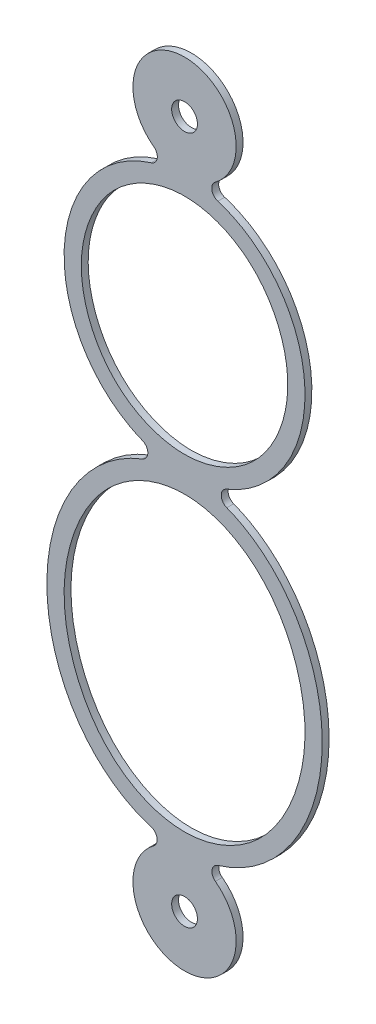
SolidWorks part; units mm, degrees
material "3.0517 (EN-AW 3003)"
ref_plane "Front Plane" through (0, 0, 0) normal (0, 0, 1) x (1, 0, 0)
ref_plane "Top Plane" through (0, 0, 0) normal (0, 1, 0) x (1, 0, 0)
ref_plane "Right Plane" through (0, 0, 0) normal (1, 0, 0) x (0, 0, -1)
sketch "Sketch1" plane through (0, 0, 0) normal (0, 0, 1) x (1, 0, 0)
  line L0 (0, 10) -> (0, -10) construction
  line L1 (-4, -3.75) -> (4, -3.75) construction
  line L2 (-3.5, 4.75) -> (3.5, 4.75) construction
  arc A0 (0.8919, 8.794) -> (-0.8919, 8.794) centre (0, 10) ccw
  circle A1 centre (0, 10) radius 0.375
  arc A2 (-0.8961, -8.7971) -> (0.8961, -8.7971) centre (0, -10) ccw
  circle A3 centre (0, -10) radius 0.375
  arc A4 (1.2236, 1.2366) -> (1.227, 0.771) centre (1.3164, 1.0045) ccw
  arc A5 (0.8919, 8.794) -> (0.967, 8.354) centre (1.0406, 8.593) ccw
  arc A6 (0.974, -8.357) -> (0.8961, -8.7971) centre (1.0455, -8.5966) ccw
  arc A7 (-0.967, 8.354) -> (-0.8919, 8.794) centre (-1.0406, 8.593) ccw
  arc A8 (-1.227, 0.771) -> (-1.2236, 1.2366) centre (-1.3164, 1.0045) ccw
  arc A9 (-0.8961, -8.7971) -> (-0.974, -8.357) centre (-1.0455, -8.5966) ccw
  ellipse E0 centre (0, -3.75) end of major axis (0, -8.5) minor radius 4 (0.974, -8.357) -> (1.227, 0.771) ccw
  ellipse E1 centre (0, 4.75) end of major axis (0, 8.5) minor radius 3.5 (1.2236, 1.2366) -> (0.967, 8.354) ccw
  ellipse E2 centre (0, -3.75) end of major axis (0, -8.5) minor radius 4 (-1.227, 0.771) -> (-0.974, -8.357) ccw
  ellipse E3 centre (0, 4.75) end of major axis (0, 8.5) minor radius 3.5 (-0.967, 8.354) -> (-1.2236, 1.2366) ccw
  spline S1 degree 3 poles (-2.3303, 2.182) (0, 1.159) (2.3303, 2.182) (3.3348, 4.75) (2.3303, 7.318) (0, 8.341) (-2.3303, 7.318) (-3.3348, 4.75) (-2.3303, 2.182) (0, 1.159) (2.3303, 2.182) knots -2.356194 -1.570796 -0.785398 0 0.785398 1.570796 2.356194 3.141593 3.926991 4.712389 5.497787 6.283185 7.068583 7.853982 8.63938 only from (0, 1.5) to (0, 1.5)
  spline S3 degree 3 poles (-2.6931, -7.1343) (0, -8.4328) (2.6931, -7.1343) (3.9035, -3.75) (2.6931, -0.3657) (0, 0.9328) (-2.6931, -0.3657) (-3.9035, -3.75) (-2.6931, -7.1343) (0, -8.4328) (2.6931, -7.1343) knots -2.356194 -1.570796 -0.785398 0 0.785398 1.570796 2.356194 3.141593 3.926991 4.712389 5.497787 6.283185 7.068583 7.853982 8.63938 only from (0, -8) to (0, -8)
  dimension "D2" = 3
  dimension "D3" = 0.75
  dimension "D4" = 8
  dimension "D5" = 7
  dimension "D8" = 0.5
  dimension "D1" = 20
  dimension "D6" = 1
extrude "Boss-Extrude1" add sketch "Sketch1" along normal mid plane 0.2
sketch "Sketch2" plane through (0, 0, 0) normal (0, 0, 1) x (1, 0, 0)
  arc A8 (-1.0406, 8.593) -> (1.0406, 8.593) centre (0, 5.2145) cw
  arc A9 (-1.0455, -8.5966) -> (1.0455, -8.5966) centre (0, -5.09) ccw
  arc A16 (-1.0455, -8.5966) -> (1.0455, -8.5966) centre (0, -10) ccw
  arc A17 (1.0406, 8.593) -> (-1.0406, 8.593) centre (0, 10) ccw
  spline S0 degree 3 poles (1903.9257, -3507.5478) (289.7163, -408.9287) (27.011, 29.4324) (-2.4572, 7.8021) (-2.7414, 7.5116) (-3.2192, 6.8444) (-3.4026, 6.4813) (-3.5971, 5.8993) (-3.6476, 5.7003) (-3.7192, 5.301) (-3.7405, 5.0994) (-3.7545, 4.6925) (-3.7467, 4.4861) (-3.7023, 4.0821) (-3.6658, 3.8829) (-3.5644, 3.4904) (-3.4988, 3.2957) (-3.3398, 2.9191) (-3.2473, 2.7387) (-3.0364, 2.3935) (-2.9181, 2.2287) (-2.6539, 1.9159) (-2.5096, 1.7702) (-2.2029, 1.5059) (-2.0396, 1.3864) (13.5785, -8.1674) (115.4937, 87.2895) (-2980.8985, 2665.0914) knots -10.874457 -10.874457 -10.874457 -10.874457 0.125 0.125 0.25 0.25 0.375 0.375 0.4375 0.4375 0.5 0.5 0.5625 0.5625 0.625 0.625 0.6875 0.6875 0.75 0.75 0.8125 0.8125 0.875 0.875 0.9375 0.9375 6.492725 6.492725 6.492725 6.492725 only from (-1.0406, 8.593) to (-1.3164, 1.0045)
  spline S1 degree 3 poles (2216.1793, -3327.1601) (203.0497, -213.2288) (19.6302, 20.3665) (-2.973, -0.1319) (-3.2868, -0.5343) (-3.7889, -1.4217) (-3.9705, -1.8927) (-4.2087, -2.8844) (-4.2605, -3.3865) (-4.2421, -4.1459) (-4.2194, -4.4012) (-4.1418, -4.9002) (-4.0871, -5.1457) (-3.9452, -5.6281) (-3.858, -5.8651) (-3.6481, -6.33) (-3.5276, -6.5527) (-3.2564, -6.9752) (-3.1056, -7.1755) (-2.7707, -7.5524) (-2.5844, -7.7304) (-2.1879, -8.0467) (-1.9773, -8.1861) (15.7469, -17.6181) (119.1337, 97.72) (-2852.0183, 2791.7154) knots -7.238931 -7.238931 -7.238931 -7.238931 0.125 0.125 0.25 0.25 0.375 0.375 0.5 0.5 0.5625 0.5625 0.625 0.625 0.6875 0.6875 0.75 0.75 0.8125 0.8125 0.875 0.875 0.9375 0.9375 5.819116 5.819116 5.819116 5.819116 only from (-1.3164, 1.0045) to (-1.0455, -8.5966)
  spline S2 degree 3 poles (-1859.3382, 3531.6341) (-167.8124, 210.1423) (-22.0845, -20.9335) (1.9694, -8.1909) (2.1831, -8.0501) (2.5809, -7.7337) (2.7638, -7.5594) (3.1007, -7.1819) (3.2553, -6.977) (3.5288, -6.5508) (3.6486, -6.3287) (3.8569, -5.8675) (3.9456, -5.627) (4.0882, -5.1415) (4.1427, -4.8954) (4.2198, -4.3968) (4.2424, -4.1429) (4.2603, -3.3812) (4.2079, -2.8811) (4.0306, -2.1426) (3.9542, -1.898) (3.7712, -1.4286) (3.6641, -1.2018) (3.2941, -0.546) (2.9766, -0.1369) (-14.3264, 15.6334) (-163.1414, -94.3327) (1669.742, -3628.5284) knots -6.625593 -6.625593 -6.625593 -6.625593 0.0625 0.0625 0.125 0.125 0.1875 0.1875 0.25 0.25 0.3125 0.3125 0.375 0.375 0.4375 0.4375 0.5 0.5 0.625 0.625 0.6875 0.6875 0.75 0.75 0.875 0.875 6.552625 6.552625 6.552625 6.552625 only from (1.0455, -8.5966) to (1.3164, 1.0045)
  spline S3 degree 3 poles (-2182.1089, 3351.3968) (-303.9875, 366.6085) (-24.3441, -21.3402) (2.666, 1.9046) (2.928, 2.216) (3.3554, 2.9155) (3.513, 3.2915) (3.6663, 3.8847) (3.7031, 4.0873) (3.747, 4.4908) (3.7545, 4.6933) (3.7405, 5.0996) (3.7187, 5.305) (3.6464, 5.7057) (3.5963, 5.9019) (3.4036, 6.478) (3.2157, 6.8492) (2.8625, 7.3425) (2.7324, 7.4979) (2.4461, 7.7894) (2.2905, 7.9244) (1.9639, 8.1643) (1.7917, 8.2706) (-14.334, 16.447) (-108.4577, -84.9417) (3192.8979, -2397.1321) knots -10.602344 -10.602344 -10.602344 -10.602344 0.125 0.125 0.25 0.25 0.375 0.375 0.4375 0.4375 0.5 0.5 0.5625 0.5625 0.625 0.625 0.75 0.75 0.8125 0.8125 0.875 0.875 0.9375 0.9375 6.428873 6.428873 6.428873 6.428873 only from (1.3164, 1.0045) to (1.0406, 8.593)
  spline S4 degree 3 poles (-1.0406, 8.593) (-1.4336, 8.4719) (-1.7949, 8.2882) (-2.4572, 7.8021) (-2.7414, 7.5116) (-3.2192, 6.8444) (-3.4026, 6.4813) (-3.5971, 5.8993) (-3.6476, 5.7003) (-3.7192, 5.301) (-3.7405, 5.0994) (-3.7545, 4.6925) (-3.7467, 4.4861) (-3.7023, 4.0821) (-3.6658, 3.8829) (-3.5644, 3.4904) (-3.4988, 3.2957) (-3.3398, 2.9191) (-3.2473, 2.7387) (-3.0364, 2.3935) (-2.9181, 2.2287) (-2.6539, 1.9159) (-2.5096, 1.7702) (-2.2029, 1.5059) (-2.0396, 1.3864) (-1.6921, 1.1738) (-1.5073, 1.0808) (-1.3164, 1.0045) knots 0 0 0 0 0.125 0.125 0.25 0.25 0.375 0.375 0.4375 0.4375 0.5 0.5 0.5625 0.5625 0.625 0.625 0.6875 0.6875 0.75 0.75 0.8125 0.8125 0.875 0.875 0.9375 0.9375 1 1 1 1
  spline S5 degree 3 poles (-1.3164, 1.0045) (-1.7947, 0.8214) (-2.2184, 0.5524) (-2.973, -0.1319) (-3.2868, -0.5343) (-3.7889, -1.4217) (-3.9705, -1.8927) (-4.2087, -2.8844) (-4.2605, -3.3865) (-4.2421, -4.1459) (-4.2194, -4.4012) (-4.1418, -4.9002) (-4.0871, -5.1457) (-3.9452, -5.6281) (-3.858, -5.8651) (-3.6481, -6.33) (-3.5276, -6.5527) (-3.2564, -6.9752) (-3.1056, -7.1755) (-2.7707, -7.5524) (-2.5844, -7.7304) (-2.1879, -8.0467) (-1.9773, -8.1861) (-1.5292, -8.4246) (-1.291, -8.5234) (-1.0455, -8.5966) knots 0 0 0 0 0.125 0.125 0.25 0.25 0.375 0.375 0.5 0.5 0.5625 0.5625 0.625 0.625 0.6875 0.6875 0.75 0.75 0.8125 0.8125 0.875 0.875 0.9375 0.9375 1 1 1 1
  spline S6 degree 3 poles (1.0455, -8.5966) (1.2906, -8.5235) (1.524, -8.4268) (1.9694, -8.1909) (2.1831, -8.0501) (2.5809, -7.7337) (2.7638, -7.5594) (3.1007, -7.1819) (3.2553, -6.977) (3.5288, -6.5508) (3.6486, -6.3287) (3.8569, -5.8675) (3.9456, -5.627) (4.0882, -5.1415) (4.1427, -4.8954) (4.2198, -4.3968) (4.2424, -4.1429) (4.2603, -3.3812) (4.2079, -2.8811) (4.0306, -2.1426) (3.9542, -1.898) (3.7712, -1.4286) (3.6641, -1.2018) (3.2941, -0.546) (2.9766, -0.1369) (2.2311, 0.5426) (1.7944, 0.8215) (1.3164, 1.0045) knots 0 0 0 0 0.0625 0.0625 0.125 0.125 0.1875 0.1875 0.25 0.25 0.3125 0.3125 0.375 0.375 0.4375 0.4375 0.5 0.5 0.625 0.625 0.6875 0.6875 0.75 0.75 0.875 0.875 1 1 1 1
  spline S7 degree 3 poles (1.3164, 1.0045) (1.6983, 1.1572) (2.0438, 1.3691) (2.666, 1.9046) (2.928, 2.216) (3.3554, 2.9155) (3.513, 3.2915) (3.6663, 3.8847) (3.7031, 4.0873) (3.747, 4.4908) (3.7545, 4.6933) (3.7405, 5.0996) (3.7187, 5.305) (3.6464, 5.7057) (3.5963, 5.9019) (3.4036, 6.478) (3.2157, 6.8492) (2.8625, 7.3425) (2.7324, 7.4979) (2.4461, 7.7894) (2.2905, 7.9244) (1.9639, 8.1643) (1.7917, 8.2706) (1.4288, 8.4546) (1.2372, 8.5324) (1.0406, 8.593) knots 0 0 0 0 0.125 0.125 0.25 0.25 0.375 0.375 0.4375 0.4375 0.5 0.5 0.5625 0.5625 0.625 0.625 0.75 0.75 0.8125 0.8125 0.875 0.875 0.9375 0.9375 1 1 1 1
  spline S10 degree 3 poles (0.1901, 7.75) (-0.1901, 7.75) (-0.3763, 7.7278) (-0.7417, 7.6436) (-0.9225, 7.5805) (-1.2624, 7.4203) (-1.4229, 7.3232) (-1.7248, 7.0946) (-1.8627, 6.9655) (-2.1087, 6.6828) (-2.2187, 6.5273) (-2.4077, 6.2012) (-2.4868, 6.0311) (-2.6162, 5.6776) (-2.6661, 5.4936) (-2.7326, 5.1251) (-2.75, 4.9389) (-2.75, 4.5625) (-2.7323, 4.3726) (-2.6655, 4.004) (-2.6164, 3.8232) (-2.4868, 3.4688) (-2.4066, 3.2968) (-2.2191, 2.9735) (-2.1113, 2.8206) (-1.8634, 2.5351) (-1.7248, 2.4056) (-1.4274, 2.18) (-1.2673, 2.0823) (-0.9238, 1.9198) (-0.7467, 1.8579) (-0.3817, 1.7731) (-0.1912, 1.7503) (0.1847, 1.7497) (0.3708, 1.7713) (0.7392, 1.8555) (0.9188, 1.9181) (1.2588, 2.0777) (1.4225, 2.1767) (1.7228, 2.4037) (1.8599, 2.5316) (2.1079, 2.816) (2.2179, 2.9716) (2.4065, 3.2965) (2.4866, 3.4681) (2.6165, 3.8235) (2.6656, 4.0046) (2.7324, 4.3735) (2.7501, 4.5633) (2.7499, 4.9403) (2.7324, 5.1266) (2.6657, 5.4951) (2.6157, 5.679) (2.4862, 6.0326) (2.4071, 6.2022) (2.219, 6.5267) (2.1085, 6.683) (1.8623, 6.9659) (1.7261, 7.0933) (1.428, 7.3196) (1.2641, 7.4193) (0.9247, 7.5796) (0.748, 7.6418) (0.3796, 7.7274) (0.1901, 7.75) (-0.1901, 7.75) (-0.3763, 7.7278) knots -0.03125 -0.03125 0 0 0.03125 0.03125 0.0625 0.0625 0.09375 0.09375 0.125 0.125 0.15625 0.15625 0.1875 0.1875 0.21875 0.21875 0.25 0.25 0.28125 0.28125 0.3125 0.3125 0.34375 0.34375 0.375 0.375 0.40625 0.40625 0.4375 0.4375 0.46875 0.46875 0.5 0.5 0.53125 0.53125 0.5625 0.5625 0.59375 0.59375 0.625 0.625 0.65625 0.65625 0.6875 0.6875 0.71875 0.71875 0.75 0.75 0.78125 0.78125 0.8125 0.8125 0.84375 0.84375 0.875 0.875 0.90625 0.90625 0.9375 0.9375 0.96875 0.96875 1 1 1.03125 1.03125 1.0625 only from (0, 7.75) to (0, 7.75)
  spline S11 degree 3 poles (0.1901, 7.75) (-0.1901, 7.75) (-0.3763, 7.7278) (-0.7417, 7.6436) (-0.9225, 7.5805) (-1.2624, 7.4203) (-1.4229, 7.3232) (-1.7248, 7.0946) (-1.8627, 6.9655) (-2.1087, 6.6828) (-2.2187, 6.5273) (-2.4077, 6.2012) (-2.4868, 6.0311) (-2.6162, 5.6776) (-2.6661, 5.4936) (-2.7326, 5.1251) (-2.75, 4.9389) (-2.75, 4.5625) (-2.7323, 4.3726) (-2.6655, 4.004) (-2.6164, 3.8232) (-2.4868, 3.4688) (-2.4066, 3.2968) (-2.2191, 2.9735) (-2.1113, 2.8206) (-1.8634, 2.5351) (-1.7248, 2.4056) (-1.4274, 2.18) (-1.2673, 2.0823) (-0.9238, 1.9198) (-0.7467, 1.8579) (-0.3817, 1.7731) (-0.1912, 1.7503) (0.1847, 1.7497) (0.3708, 1.7713) (0.7392, 1.8555) (0.9188, 1.9181) (1.2588, 2.0777) (1.4225, 2.1767) (1.7228, 2.4037) (1.8599, 2.5316) (2.1079, 2.816) (2.2179, 2.9716) (2.4065, 3.2965) (2.4866, 3.4681) (2.6165, 3.8235) (2.6656, 4.0046) (2.7324, 4.3735) (2.7501, 4.5633) (2.7499, 4.9403) (2.7324, 5.1266) (2.6657, 5.4951) (2.6157, 5.679) (2.4862, 6.0326) (2.4071, 6.2022) (2.219, 6.5267) (2.1085, 6.683) (1.8623, 6.9659) (1.7261, 7.0933) (1.428, 7.3196) (1.2641, 7.4193) (0.9247, 7.5796) (0.748, 7.6418) (0.3796, 7.7274) (0.1901, 7.75) (-0.1901, 7.75) (-0.3763, 7.7278) knots -0.03125 -0.03125 0 0 0.03125 0.03125 0.0625 0.0625 0.09375 0.09375 0.125 0.125 0.15625 0.15625 0.1875 0.1875 0.21875 0.21875 0.25 0.25 0.28125 0.28125 0.3125 0.3125 0.34375 0.34375 0.375 0.375 0.40625 0.40625 0.4375 0.4375 0.46875 0.46875 0.5 0.5 0.53125 0.53125 0.5625 0.5625 0.59375 0.59375 0.625 0.625 0.65625 0.65625 0.6875 0.6875 0.71875 0.71875 0.75 0.75 0.78125 0.78125 0.8125 0.8125 0.84375 0.84375 0.875 0.875 0.90625 0.90625 0.9375 0.9375 0.96875 0.96875 1 1 1.03125 1.03125 1.0625 only from (0, 7.75) to (0, 7.75)
  spline S13 degree 3 poles (0.2405, 0.25) (-0.2405, 0.25) (-0.4749, 0.2165) (-0.9329, 0.0898) (-1.1558, -0.0042) (-1.5683, -0.2385) (-1.763, -0.3816) (-2.1137, -0.7029) (-2.2704, -0.8811) (-2.6905, -1.4635) (-2.8935, -1.8914) (-3.1762, -2.8029) (-3.2498, -3.272) (-3.2501, -3.9867) (-3.2311, -4.2254) (-3.1591, -4.6923) (-3.1061, -4.9223) (-2.966, -5.3755) (-2.8782, -5.5995) (-2.6709, -6.0256) (-2.5511, -6.2293) (-2.2734, -6.615) (-2.1142, -6.7965) (-1.7651, -7.1166) (-1.5723, -7.2589) (-1.1571, -7.4954) (-0.9396, -7.5873) (-0.4832, -7.7148) (-0.2423, -7.7495) (0.1124, -7.7503) (0.2305, -7.7423) (0.4663, -7.7103) (0.5848, -7.6859) (0.93, -7.591) (1.1494, -7.4991) (1.5676, -7.2623) (1.7591, -7.1216) (2.1108, -6.8002) (2.2702, -6.6189) (2.5484, -6.2337) (2.6701, -6.0272) (2.879, -5.5979) (2.9652, -5.3775) (3.175, -4.7006) (3.2501, -4.2215) (3.25, -3.5133) (3.2315, -3.2777) (3.1592, -2.8077) (3.105, -2.5735) (2.9649, -2.1215) (2.8787, -1.9017) (2.6714, -1.4753) (2.549, -1.2672) (2.2711, -0.8821) (2.1149, -0.704) (1.7626, -0.3812) (1.5691, -0.2391) (1.1589, -0.0057) (0.9378, 0.0882) (0.4765, 0.2163) (0.2405, 0.25) (-0.2405, 0.25) (-0.4749, 0.2165) knots -0.03125 -0.03125 0 0 0.03125 0.03125 0.0625 0.0625 0.09375 0.09375 0.125 0.125 0.1875 0.1875 0.25 0.25 0.28125 0.28125 0.3125 0.3125 0.34375 0.34375 0.375 0.375 0.40625 0.40625 0.4375 0.4375 0.46875 0.46875 0.5 0.5 0.515625 0.515625 0.53125 0.53125 0.5625 0.5625 0.59375 0.59375 0.625 0.625 0.65625 0.65625 0.6875 0.6875 0.75 0.75 0.78125 0.78125 0.8125 0.8125 0.84375 0.84375 0.875 0.875 0.90625 0.90625 0.9375 0.9375 0.96875 0.96875 1 1 1.03125 1.03125 1.0625 only from (0, 0.25) to (0, 0.25)
  spline S14 degree 3 poles (0.2405, 0.25) (-0.2405, 0.25) (-0.4749, 0.2165) (-0.9329, 0.0898) (-1.1558, -0.0042) (-1.5683, -0.2385) (-1.763, -0.3816) (-2.1137, -0.7029) (-2.2704, -0.8811) (-2.6905, -1.4635) (-2.8935, -1.8914) (-3.1762, -2.8029) (-3.2498, -3.272) (-3.2501, -3.9867) (-3.2311, -4.2254) (-3.1591, -4.6923) (-3.1061, -4.9223) (-2.966, -5.3755) (-2.8782, -5.5995) (-2.6709, -6.0256) (-2.5511, -6.2293) (-2.2734, -6.615) (-2.1142, -6.7965) (-1.7651, -7.1166) (-1.5723, -7.2589) (-1.1571, -7.4954) (-0.9396, -7.5873) (-0.4832, -7.7148) (-0.2423, -7.7495) (0.1124, -7.7503) (0.2305, -7.7423) (0.4663, -7.7103) (0.5848, -7.6859) (0.93, -7.591) (1.1494, -7.4991) (1.5676, -7.2623) (1.7591, -7.1216) (2.1108, -6.8002) (2.2702, -6.6189) (2.5484, -6.2337) (2.6701, -6.0272) (2.879, -5.5979) (2.9652, -5.3775) (3.175, -4.7006) (3.2501, -4.2215) (3.25, -3.5133) (3.2315, -3.2777) (3.1592, -2.8077) (3.105, -2.5735) (2.9649, -2.1215) (2.8787, -1.9017) (2.6714, -1.4753) (2.549, -1.2672) (2.2711, -0.8821) (2.1149, -0.704) (1.7626, -0.3812) (1.5691, -0.2391) (1.1589, -0.0057) (0.9378, 0.0882) (0.4765, 0.2163) (0.2405, 0.25) (-0.2405, 0.25) (-0.4749, 0.2165) knots -0.03125 -0.03125 0 0 0.03125 0.03125 0.0625 0.0625 0.09375 0.09375 0.125 0.125 0.1875 0.1875 0.25 0.25 0.28125 0.28125 0.3125 0.3125 0.34375 0.34375 0.375 0.375 0.40625 0.40625 0.4375 0.4375 0.46875 0.46875 0.5 0.5 0.515625 0.515625 0.53125 0.53125 0.5625 0.5625 0.59375 0.59375 0.625 0.625 0.65625 0.65625 0.6875 0.6875 0.75 0.75 0.78125 0.78125 0.8125 0.8125 0.84375 0.84375 0.875 0.875 0.90625 0.90625 0.9375 0.9375 0.96875 0.96875 1 1 1.03125 1.03125 1.0625 only from (0, 0.25) to (0, 0.25)
  dimension "D2" = 0.25
  dimension "D1" = 0.25
  dimension "D3" = 0.25
extrude "Boss-Extrude2" [suppressed] add sketch "Sketch2" along normal mid plane 0.6
